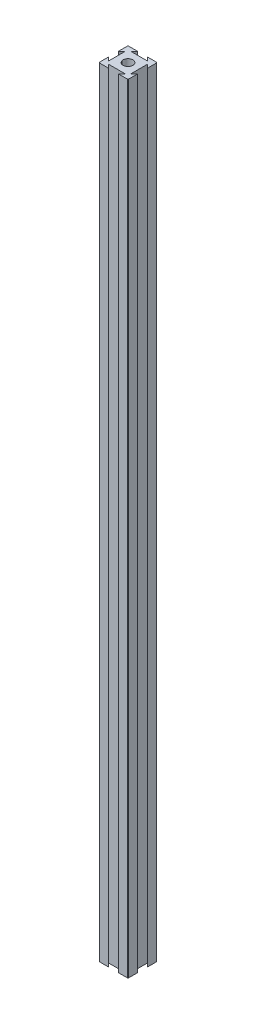
SolidWorks part; units mm, degrees
material "Alumina"
ref_plane "Front Plane" through (0, 0, 0) normal (0, 0, 1) x (1, 0, 0)
ref_plane "Top Plane" through (0, 0, 0) normal (0, 1, 0) x (1, 0, 0)
ref_plane "Right Plane" through (0, 0, 0) normal (1, 0, 0) x (0, 0, -1)
sketch "Sketch1" plane through (0, 0, 0) normal (0, 1, 0) x (1, 0, 0)
  line L0 (6.6667, 20) -> (4.285, 17.6183)
  line L1 (0, 0) -> (20, 0)
  line L2 (0, 0) -> (0, 20)
  line L3 (0, 20) -> (20, 20)
  line L4 (20, 0) -> (20, 20)
  line L5 (4.285, 17.6183) -> (15.715, 17.6183)
  line L6 (15.715, 17.6183) -> (13.3333, 20)
  line L7 (13.3333, 20) -> (6.6667, 20)
  line L8 (0, 10) -> (20, 10) construction
  line L9 (10, 20) -> (10, 0) construction
  line L10 (15.715, 2.3817) -> (13.3333, 0)
  line L11 (4.285, 2.3817) -> (15.715, 2.3817)
  line L12 (6.6667, 0) -> (4.285, 2.3817)
  line L13 (13.3333, 0) -> (6.6667, 0)
  line L14 (0, 13.3333) -> (2.3817, 15.715)
  line L15 (2.3817, 15.715) -> (2.3817, 4.285)
  line L16 (2.3817, 4.285) -> (0, 6.6667)
  line L17 (0, 6.6667) -> (0, 13.3333)
  line L18 (17.6183, 4.285) -> (20, 6.6667)
  line L19 (17.6183, 15.715) -> (17.6183, 4.285)
  line L20 (20, 13.3333) -> (17.6183, 15.715)
  line L21 (20, 6.6667) -> (20, 13.3333)
  circle A0 centre (10, 10) radius 3.3333
  dimension "D1" = 20
  dimension "D2" = 20
  dimension "D3" = 6.6667
  dimension "D4" = 6.6667
  dimension "D5" = 45
  dimension "D6" = 45
  dimension "D7" = 11.43
  dimension "D8" = 6.6667
  dimension "D9" = 6.6667
  dimension "D10" = 11.43
  dimension "D11" = 45
  dimension "D12" = 45
extrude "Boss-Extrude1" add sketch "Sketch1" along normal blind 533.4 contours L20 L4 L3 L6 L5 L0 L2 L14 L15 L16 L1 L12 L11 L10 L18 L19 A0
fillet "Fillet4" radius 0.508 4 edges at (0, 266.7, -20) (20, 266.7, -20) (0, 266.7, 0) (20, 266.7, 0)
